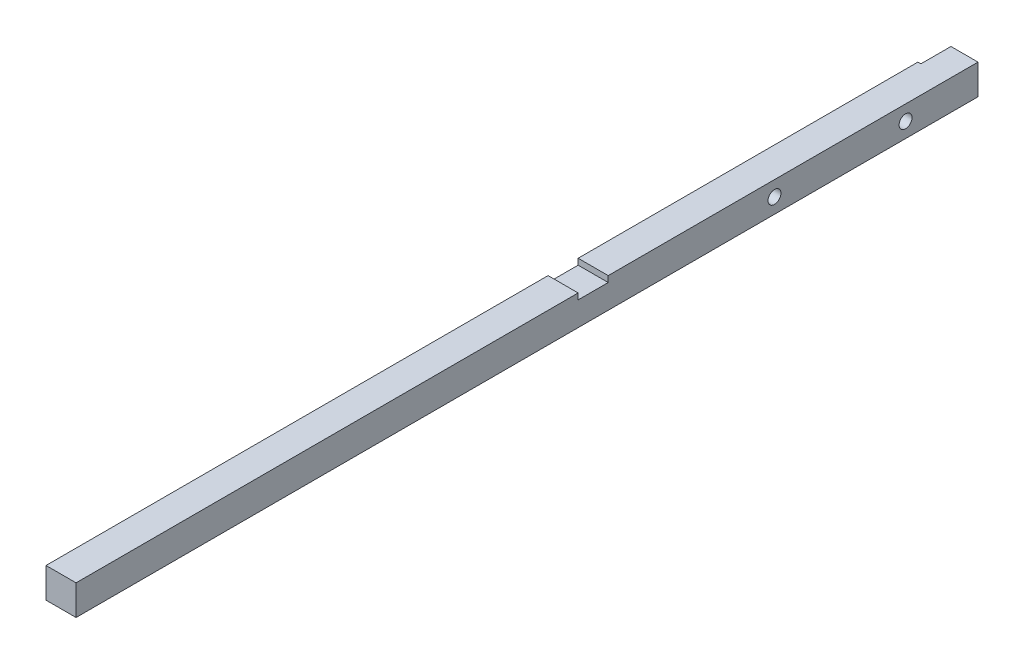
SolidWorks part; units mm, degrees
ref_plane "Plan de face" through (0, 0, 0) normal (0, 0, 1) x (1, 0, 0)
ref_plane "Plan de dessus" through (0, 0, 0) normal (0, 1, 0) x (1, 0, 0)
ref_plane "Plan de droite" through (0, 0, 0) normal (1, 0, 0) x (0, 0, -1)
sketch "Esquisse1" plane through (0, 0, 0) normal (0, 0, 1) x (1, 0, 0)
  line L0 (-5, 5) -> (5, -5) construction
  line L1 (-5, 5) -> (5, 5)
  line L2 (-5, 5) -> (-5, -5)
  line L3 (-5, -5) -> (5, -5)
  line L4 (5, 5) -> (5, -5)
  dimension "D1" = 10
extrude "Boss.-Extru.1" add sketch "Esquisse1" along normal offset from surface (300 mm away) 2 from vertex at 7
sketch "Esquisse4" plane through (5, 0, 0) normal (1, 0, 0) x (0, 0, -1)
  line L0 (-140, 239) -> (-140, 3) construction
  line L1 (-140, 5) -> (-130, 5)
  line L2 (-140, 5) -> (-140, 3)
  line L3 (-140, 3) -> (-130, 3)
  line L4 (-130, 5) -> (-130, 3)
  line L5 (-130, 239) -> (-130, 3) construction
  line L6 (-307, 5) -> (-7, 5) construction
  dimension "D1" = 2
extrude "Enlèv. mat.-Extru.3" cut sketch "Esquisse4" against normal through all
sketch "Esquisse5" plane through (5, 0, 0) normal (1, 0, 0) x (0, 0, -1)
  line L0 (-307, -5) -> (-7, -5) construction
  line L1 (-130, -5) -> (-140, -5)
  line L2 (-130, -5) -> (-130, -3)
  line L3 (-130, -3) -> (-140, -3)
  line L4 (-140, -5) -> (-140, -3)
  line L7 (-140, 3) -> (-140, 239) construction
  line L8 (-130, 3) -> (-130, 239) construction
  dimension "D1" = 2
extrude "Enlèv. mat.-Extru.4" [suppressed] cut sketch "Esquisse5" against normal through all
sketch "Esquisse6" plane through (-5, 0, 0) normal (-1, 0, 0) x (0, 0, 1)
  line L1 (7, -5) -> (17, -5)
  line L2 (7, -5) -> (7, 5)
  line L3 (7, 5) -> (17, 5)
  line L4 (17, -5) -> (17, 5)
extrude "Enlèv. mat.-Extru.5" cut sketch "Esquisse6" against normal blind 1
hole_wizard "Dégagement M41" positions "Esquisse8" profile "Esquisse9" hole size "M4" standard "Ansi Metric" end condition through all
sketch "Esquisse8" plane through (-5, 0, 0) normal (-1, 0, 0) x (0, 0, 1)
  point P0 (74.69, 0)
  point P5 (31.09, 0)
sketch "Esquisse9" plane through (-5, 0, 74.69) normal (0, 1, 0) x (0, 0, 1)
  line L0 (0, 0) -> (0, 10)
  line L1 (0, 10) -> (2.15, 10)
  line L2 (2.15, 10) -> (2.15, 0)
  line L5 (2.15, 0) -> (0, 0)
  line L11 (0, -6.35) -> (0, 107.95) construction
  dimension "Diamètre du perçage jusqu'au prochain" = 4.3
  dimension "Profondeur du perçage jusqu'au prochain" = 10
